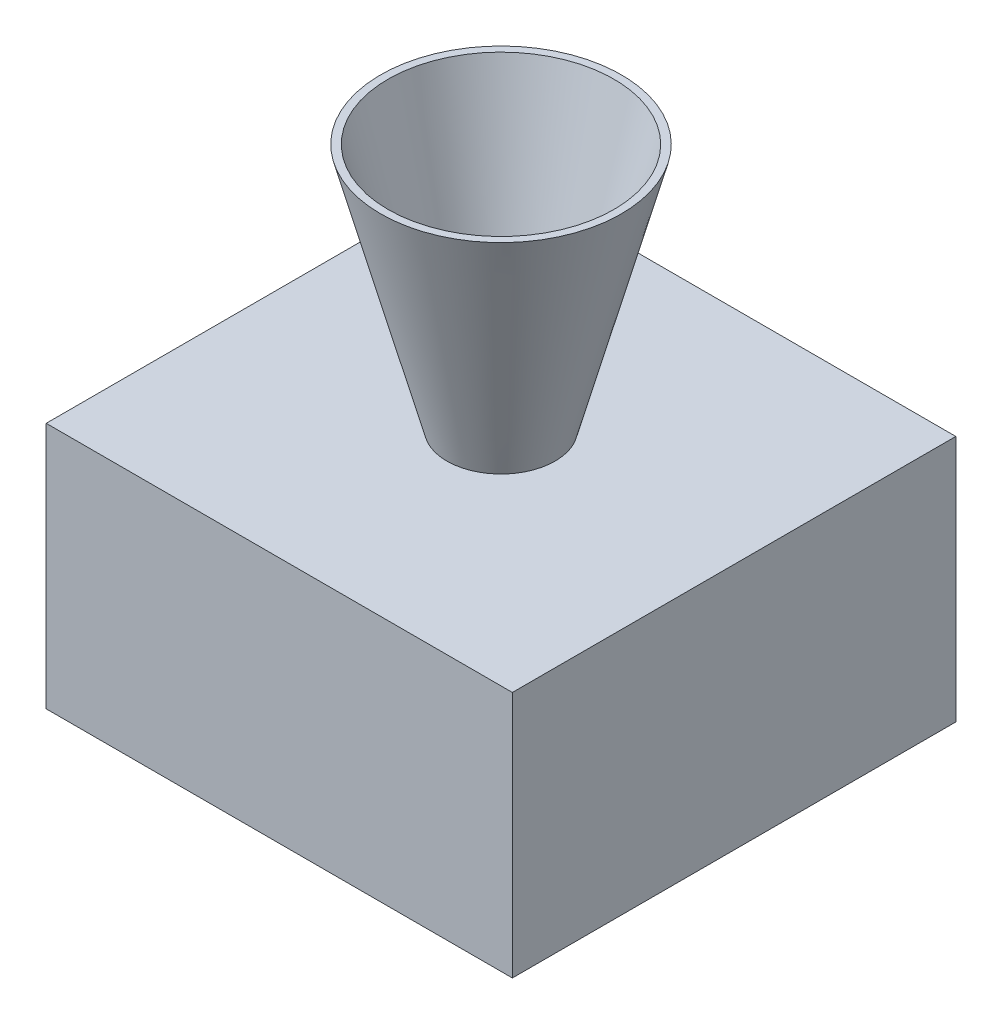
SolidWorks part; units mm, degrees
ref_plane "Front Plane" through (0, 0, 0) normal (0, 0, 1) x (1, 0, 0)
ref_plane "Top Plane" through (0, 0, 0) normal (0, 1, 0) x (1, 0, 0)
ref_plane "Right Plane" through (0, 0, 0) normal (1, 0, 0) x (0, 0, -1)
sketch "Sketch1" plane through (0, 0, 0) normal (0, 1, 0) x (1, 0, 0)
  line L1 (-82, 78) -> (82, 78)
  line L2 (-82, 78) -> (-82, -78)
  line L3 (-82, -78) -> (82, -78)
  line L4 (82, 78) -> (82, -78)
  line L5 (-82, 78) -> (82, -78) construction
  line L6 (-82, -78) -> (82, 78) construction
  point P0 (0, 0)
  dimension "D1" = 164
  dimension "D2" = 156
extrude "Boss-Extrude2" add sketch "Sketch1" along normal blind 87 contours L1 L4 L3 L2
sketch "Sketch2" plane through (0, 87, 0) normal (0, 1, 0) x (1, 0, 0)
  circle A0 centre (0, 0) radius 19.05
extrude "Boss-Extrude3" add sketch "Sketch2" along normal blind 87 draft 15 contours A0 draft outward yes
shell "Shell1" thickness 2.54
